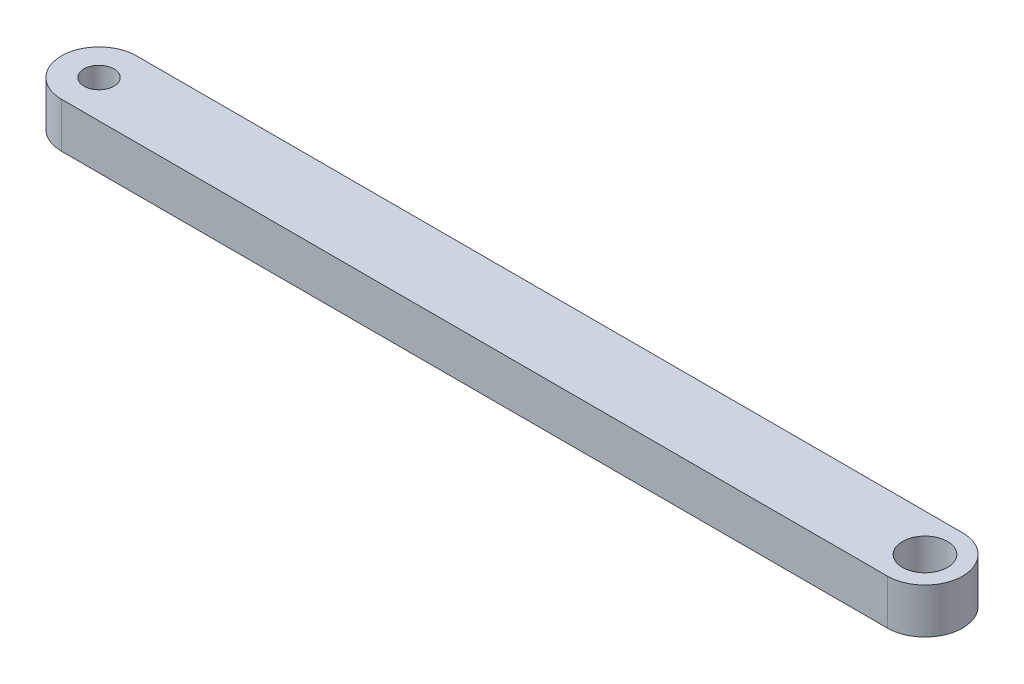
SolidWorks part; units mm, degrees
ref_plane "Front Plane" through (0, 0, 0) normal (0, 0, 1) x (1, 0, 0)
ref_plane "Top Plane" through (0, 0, 0) normal (0, 1, 0) x (1, 0, 0)
ref_plane "Right Plane" through (0, 0, 0) normal (1, 0, 0) x (0, 0, -1)
ref_plane "Plane1" through (0, 0, 0) normal (0, -1, 0) x (1, 0, 0)
sketch "Sketch1" plane through (0, 0, 0) normal (0, -1, 0) x (1, 0, 0)
  line L0 (46, 2.5) -> (-9, 2.5)
  line L1 (-9, -2.5) -> (46, -2.5)
  line L2 (46.0474, 0.0263) -> (47.1759, -2.0088) construction
  line L3 (-9.201, 8.4646) -> (-1.9265, -4.6535) construction
  line L4 (46.0474, 0.0263) -> (45.3685, -0.3502) construction
  arc A0 (-9, 2.5) -> (-9, -2.5) centre (-9, 0) ccw
  arc A1 (46, -2.5) -> (46, 2.5) centre (46, 0) ccw
  circle A2 centre (46, 0) radius 1.5
  circle A3 centre (-9, 0) radius 1
  point P9 (-11.5, 0)
  point P10 (48.5, 0)
  point P18 (52.9209, -8.4622)
  dimension "D1" = 2
  dimension "D2" = 3
  dimension "D3" = 2.5
  dimension "D4" = 55
  dimension "D5" = 9
extrude "Boss-Extrude1" add sketch "Sketch1" against normal blind 3
